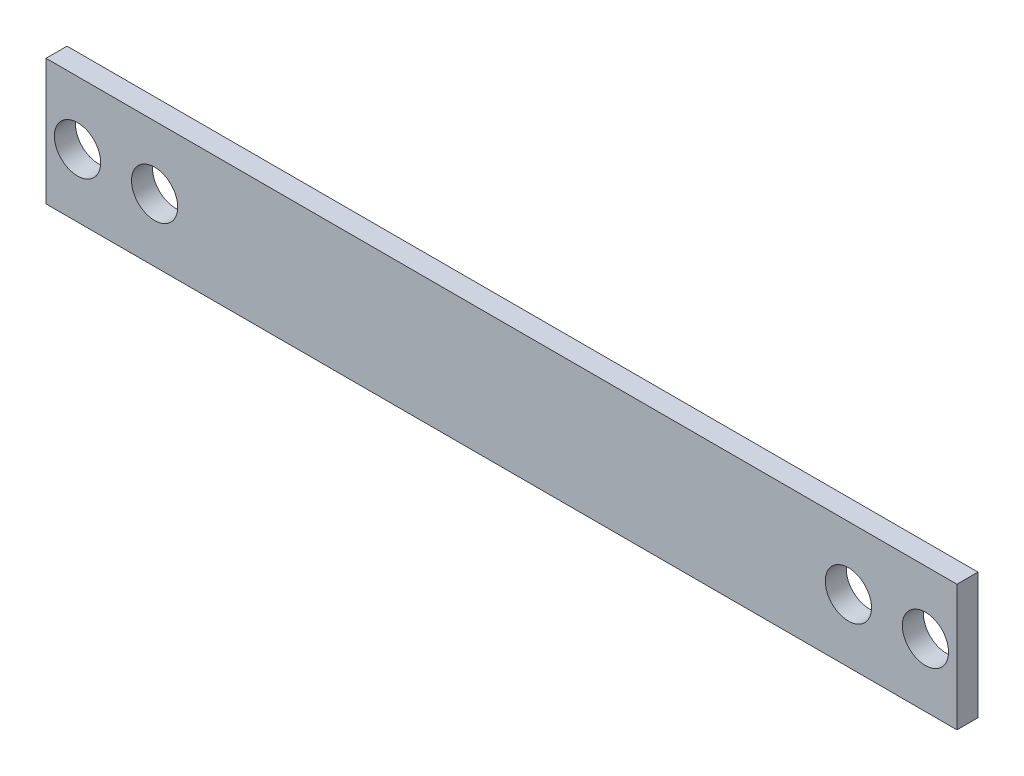
SolidWorks part; units mm, degrees
ref_plane "Front Plane" through (0, 0, 0) normal (0, 0, 1) x (1, 0, 0)
ref_plane "Top Plane" through (0, 0, 0) normal (0, 1, 0) x (1, 0, 0)
ref_plane "Right Plane" through (0, 0, 0) normal (1, 0, 0) x (0, 0, -1)
sketch "Sketch1" plane through (0, 0, 0) normal (0, 0, 1) x (1, 0, 0)
  line L0 (-30.25, 0) -> (30.25, 0) construction
  line L1 (30.25, 0) -> (38.2103, -0.4375) construction
  line L3 (-32.5, 4.5) -> (32.5, 4.5)
  line L4 (-32.5, 4.5) -> (-32.5, -4.5)
  line L5 (-32.5, -4.5) -> (32.5, -4.5)
  line L6 (32.5, 4.5) -> (32.5, -4.5)
  line L7 (-32.5, 4.5) -> (32.5, -4.5) construction
  line L8 (-32.5, -4.5) -> (32.5, 4.5) construction
  circle A0 centre (-30.25, 0) radius 1.65
  circle A1 centre (24.75, 0) radius 1.65
  circle A2 centre (30.25, 0) radius 1.65
  circle A3 centre (-24.75, 0) radius 1.65
  point P9 (0, 0)
  dimension "D1" = 3.3
  dimension "D2" = 3.3
  dimension "D4" = 3.3
  dimension "D5" = 3.3
  dimension "D3" = 55
  dimension "D6" = 5.5
  dimension "D7" = 5.5
  dimension "D8" = 9
  dimension "D9" = 65
extrude "Boss-Extrude1" add sketch "Sketch1" along normal blind 1.5
